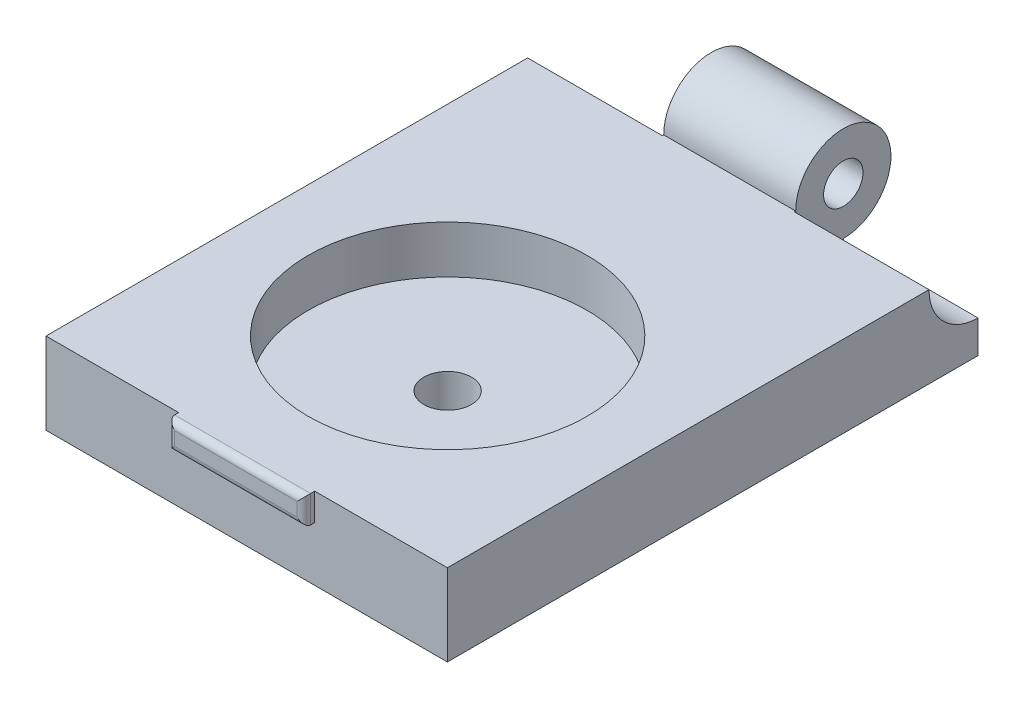
SolidWorks part; units mm, degrees
ref_plane "Frontal Plane" through (0, 0, 0) normal (0, 0, 1) x (1, 0, 0)
ref_plane "Horizontal Plane" through (0, 0, 0) normal (0, 1, 0) x (1, 0, 0)
ref_plane "Profile Plane" through (0, 0, 0) normal (1, 0, 0) x (0, 0, -1)
sketch "Sketch2" plane through (0, 0, 0) normal (0, 1, 0) x (1, 0, 0)
  line L1 (-11.4406, 17.1916) -> (18.0594, 17.1916)
  line L2 (-11.4406, 17.1916) -> (-11.4406, -21.8084)
  line L3 (-11.4406, -21.8084) -> (18.0594, -21.8084)
  line L4 (18.0594, 17.1916) -> (18.0594, -21.8084)
  dimension "D1" = 29.5
  dimension "D2" = 39
extrude "Boss-Extrude1" add sketch "Sketch2" along normal blind 6
sketch "Sketch3" plane through (0, 6, 0) normal (0, 1, 0) x (1, 0, 0)
  line L0 (-11.4406, -21.8084) -> (18.0594, -21.8084) construction
  circle A0 centre (3.3094, -7.0384) radius 10.25
  point P4 (3.3094, -21.8084)
  dimension "D1" = 20.5
extrude "Cut-Extrude1" cut sketch "Sketch3" against normal blind 3.5
sketch "Sketch4" plane through (0, 2.5, 0) normal (0, 1, 0) x (1, 0, 0)
  circle A0 centre (3.3094, -7.0384) radius 1.75
  dimension "D1" = 3.5
extrude "Cut-Extrude2" cut sketch "Sketch4" against normal through all
sketch "Sketch5" plane through (18.0594, 0, 0) normal (1, 0, 0) x (0, 0, -1)
  circle A0 centre (17.1916, 6) radius 3.6
  dimension "D1" = 7.2
extrude "Cut-Extrude3" cut sketch "Sketch5" against normal blind 9.9
sketch "Sketch6" plane through (-11.4406, 0, 0) normal (-1, 0, 0) x (0, 0, 1)
  circle A0 centre (-17.1916, 6) radius 3.6
  dimension "D1" = 7.2
extrude "Cut-Extrude4" cut sketch "Sketch6" against normal blind 9.9
sketch "Sketch7" plane through (-1.5406, 0, 0) normal (-1, 0, 0) x (0, 0, 1)
  circle A0 centre (-17.1916, 6) radius 3.5
  dimension "D1" = 7
extrude "Boss-Extrude2" add sketch "Sketch7" against normal up to surface (9.7 mm away) up to face at (8.1594, 4.5515, -15.7431)
sketch "Sketch8" plane through (8.1594, 0, 0) normal (1, 0, 0) x (0, 0, -1)
  circle A0 centre (17.1916, 6) radius 1.45
  dimension "D1" = 2.9
extrude "Cut-Extrude5" cut sketch "Sketch8" against normal up to next
sketch "Sketch9" plane through (0, 0, 21.8084) normal (0, 0, 1) x (1, 0, 0)
  line L0 (-11.4406, 6) -> (18.0594, 6) construction
  line L1 (-1.6906, 6) -> (8.3094, 6)
  line L2 (-1.6906, 6) -> (-1.6906, 4)
  line L3 (-1.6906, 4) -> (8.3094, 4)
  line L4 (8.3094, 6) -> (8.3094, 4)
  line L5 (-11.4406, 0) -> (18.0594, 0) construction
  point P6 (3.3094, 4)
  point P9 (3.3094, 0)
  dimension "D1" = 2
  dimension "D2" = 10
extrude "Boss-Extrude3" add sketch "Sketch9" along normal blind 0.8
fillet "Fillet1" radius 0.5 4 edges at (3.3094, 6, 22.6084) (8.3094, 5, 22.6084) (3.3094, 4, 22.6084) (-1.6906, 5, 22.6084)
